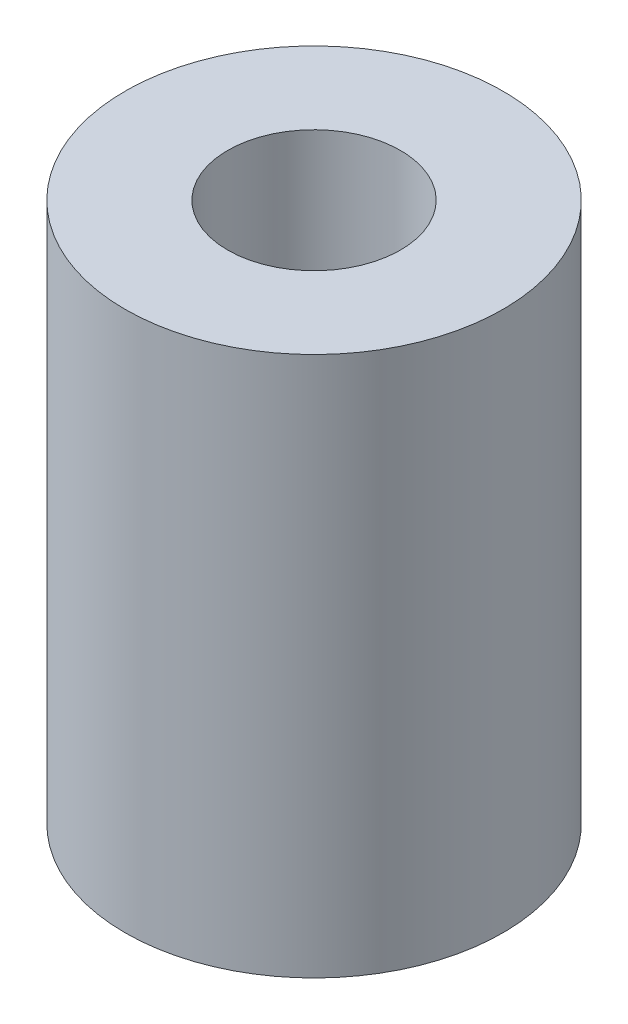
SolidWorks part; units mm, degrees
material "Nylon 101"
ref_plane "Front Plane" through (0, 0, 0) normal (0, 0, 1) x (1, 0, 0)
ref_plane "Top Plane" through (0, 0, 0) normal (0, 1, 0) x (1, 0, 0)
ref_plane "Right Plane" through (0, 0, 0) normal (1, 0, 0) x (0, 0, -1)
sketch "Sketch1" plane through (0, 0, 0) normal (0, 1, 0) x (1, 0, 0)
  circle A0 centre (0, 0) radius 3.5
  circle A1 centre (0, 0) radius 1.6
  dimension "D1" = 3.2
  dimension "D2" = 7
extrude "Boss-Extrude1" add sketch "Sketch1" along normal mid plane 10
